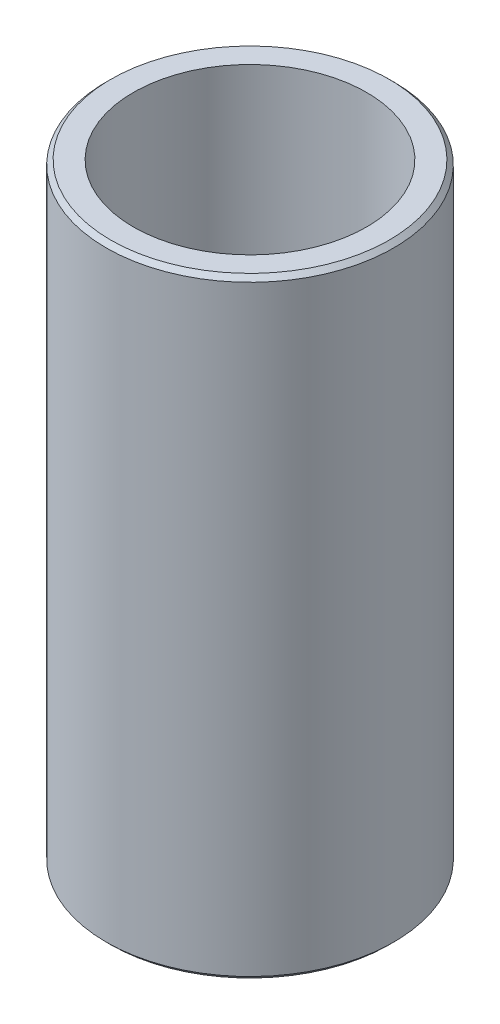
SolidWorks part; units mm, degrees
ref_plane "Front Plane" through (0, 0, 0) normal (0, 0, 1) x (1, 0, 0)
ref_plane "Top Plane" through (0, 0, 0) normal (0, 1, 0) x (1, 0, 0)
ref_plane "Right Plane" through (0, 0, 0) normal (1, 0, 0) x (0, 0, -1)
sketch "Sketch1" plane through (0, 0, 0) normal (0, 1, 0) x (1, 0, 0)
  circle A0 centre (0, 0) radius 7.94
  circle A1 centre (0, 0) radius 6.44
  dimension "D1" = 15.88
  dimension "D2" = 1.5
extrude "Boss-Extrude1" add sketch "Sketch1" along normal blind 33.7
chamfer "Chamfer1" distance 0.25 angle 45 2 edges at (0, 0, 7.94) (0, 33.7, 7.94)
